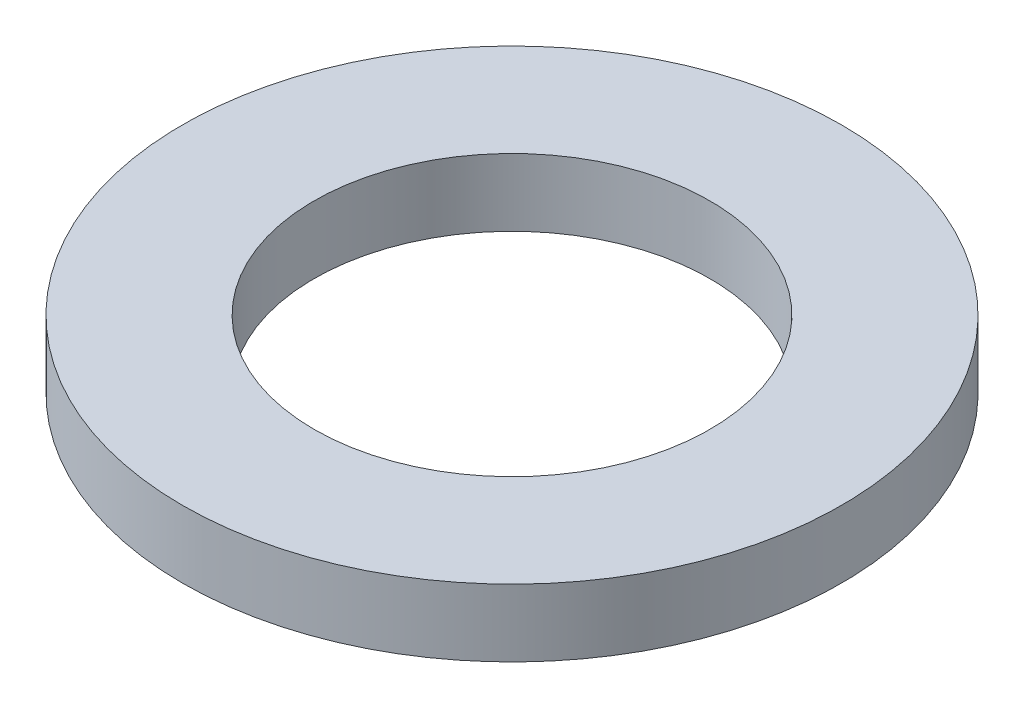
SolidWorks part; units mm, degrees
ref_plane "Front Plane" through (0, 0, 0) normal (0, 0, 1) x (1, 0, 0)
ref_plane "Top Plane" through (0, 0, 0) normal (0, 1, 0) x (1, 0, 0)
ref_plane "Right Plane" through (0, 0, 0) normal (1, 0, 0) x (0, 0, -1)
sketch "Sketch1" plane through (0, 0, 0) normal (0, 1, 0) x (1, 0, 0)
  circle A0 centre (0, 0) radius 2.3876
  circle A1 centre (0, 0) radius 3.9751
  dimension "D1" = 4.7752
  dimension "D2" = 7.9502
extrude "Boss-Extrude1" add sketch "Sketch1" along normal blind 0.8128
